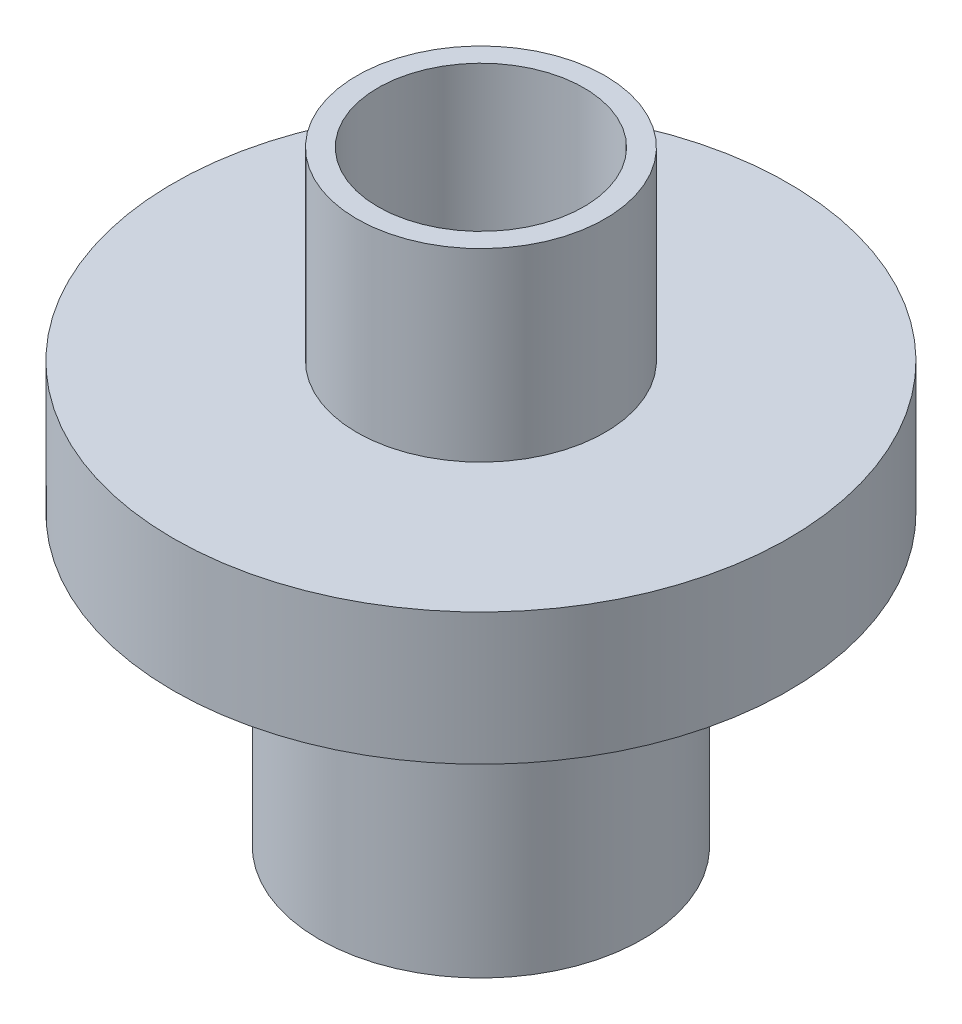
SolidWorks part; units mm, degrees
material "AISI 316 Annealed Stainless Steel Bar (SS)"
ref_plane "Front Plane" through (0, 0, 0) normal (0, 0, 1) x (1, 0, 0)
ref_plane "Top Plane" through (0, 0, 0) normal (0, 1, 0) x (1, 0, 0)
ref_plane "Right Plane" through (0, 0, 0) normal (1, 0, 0) x (0, 0, -1)
sketch "Sketch1" plane through (0, 0, 0) normal (0, 0, 1) x (1, 0, 0)
  line L0 (-7.4422, 0) -> (-7.4422, -19.7104)
  line L1 (-7.4422, -19.7104) -> (-10.2108, -19.7104)
  line L2 (-10.2108, -19.7104) -> (-10.2108, -43.7134)
  line L3 (-10.2108, -43.7134) -> (-11.684, -43.7134)
  line L4 (-11.684, -43.7134) -> (-11.684, -22.8854)
  line L5 (-11.684, -22.8854) -> (-22.225, -22.8854)
  line L6 (-22.225, -22.8854) -> (-22.225, -13.3604)
  line L7 (-22.225, -13.3604) -> (-8.9662, -13.3604)
  line L8 (-8.9662, -13.3604) -> (-8.9662, 0)
  line L9 (-8.9662, 0) -> (-7.4422, 0)
  line L10 (0, 0) -> (0, -14.9833) construction
  dimension "D1" = 7.4422
  dimension "D2" = 10.2108
  dimension "D3" = 1.524
  dimension "D4" = 11.684
  dimension "D5" = 9.525
  dimension "D6" = 19.7104
  dimension "D7" = 24.003
  dimension "D8" = 6.35
  dimension "D9" = 22.225
revolve "Revolve1" add sketch "Sketch1" angle 360 about L10
